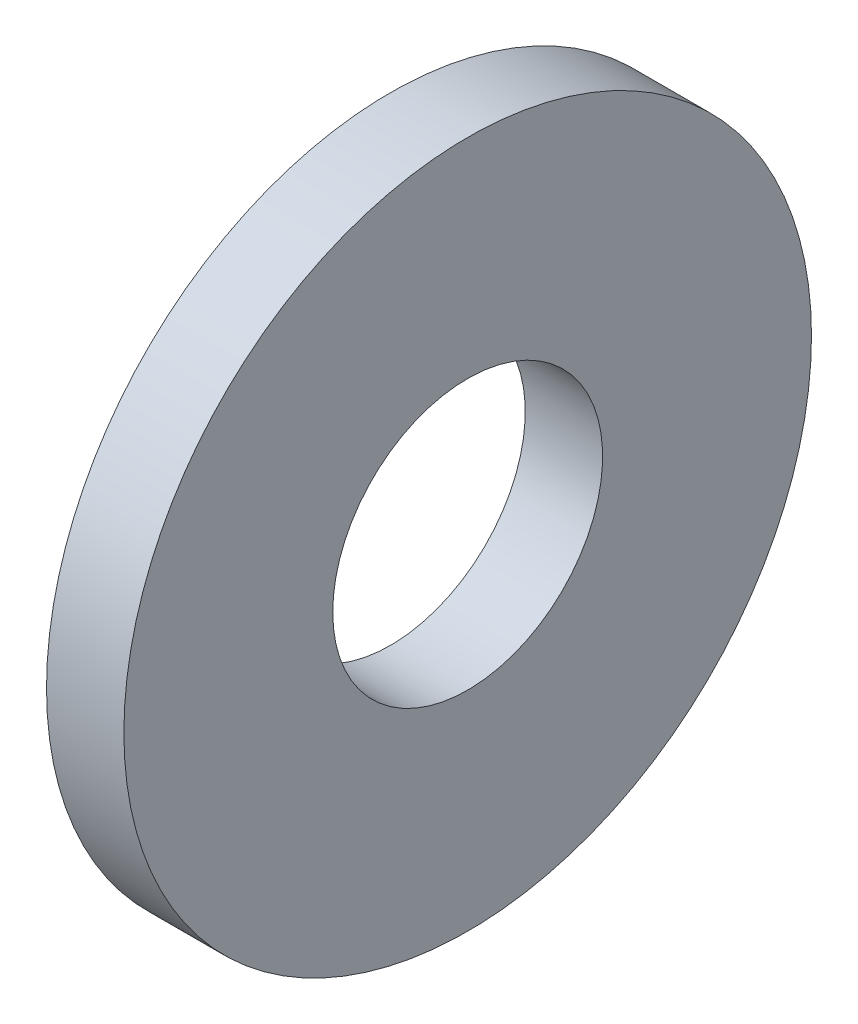
SolidWorks part; units mm, degrees
ref_plane "Plane1" through (0, 0, 0) normal (0, 0, 1) x (1, 0, 0)
ref_plane "Plane2" through (0, 0, 0) normal (0, 1, 0) x (1, 0, 0)
ref_plane "Plane3" through (0, 0, 0) normal (1, 0, 0) x (0, 0, -1)
sketch "Sketch1" plane through (0, 0, 0) normal (0, 0, 1) x (1, 0, 0)
  line L0 (-34.925, 0) -> (9.525, 0) construction
  line L1 (0, 1.57) -> (0, 4)
  line L2 (0, 4) -> (-0.9, 4)
  line L3 (-0.9, 4) -> (-0.9, 1.57)
  line L4 (-0.9, 1.57) -> (0, 1.57)
  dimension "Thickness" = 0.9
  dimension "Inside_dia" = 3.14
  dimension "Outside_dia" = 8
revolve "Base-Revolve" add sketch "Sketch1" angle 360 about L0
